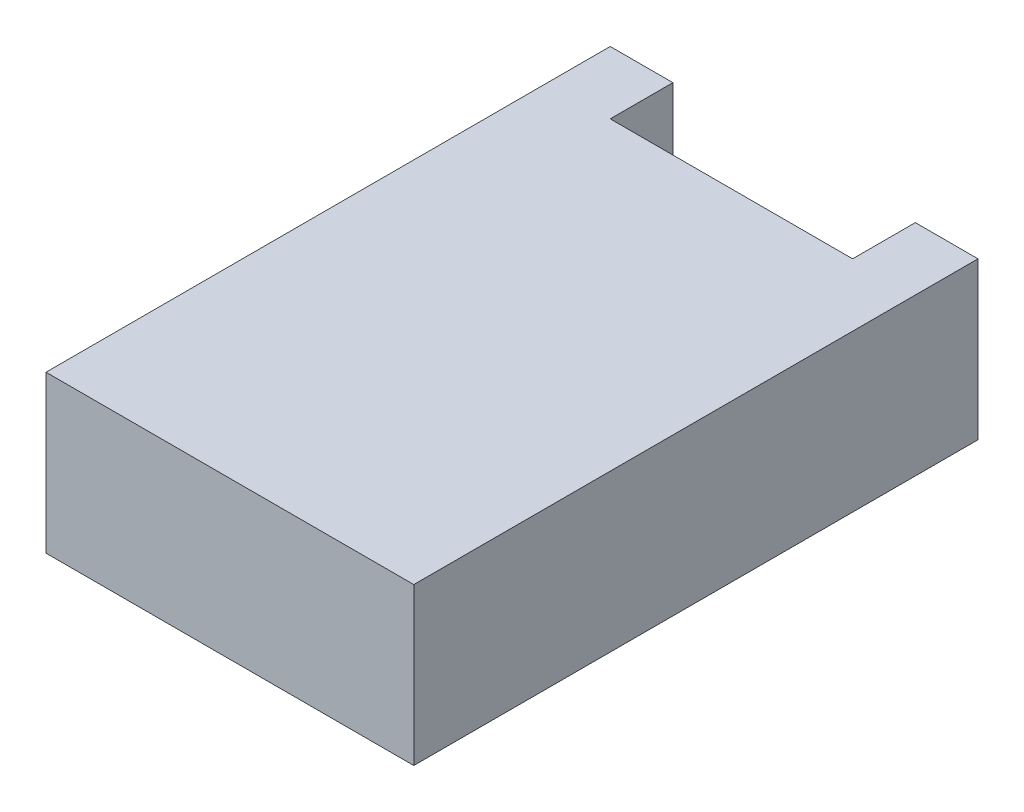
SolidWorks part; units mm, degrees
ref_plane "Front Plane" through (0, 0, 0) normal (0, 0, 1) x (1, 0, 0)
ref_plane "Top Plane" through (0, 0, 0) normal (0, 1, 0) x (1, 0, 0)
ref_plane "Right Plane" through (0, 0, 0) normal (1, 0, 0) x (0, 0, -1)
sketch "Sketch1" plane through (0, 0, 0) normal (0, 1, 0) x (1, 0, 0)
  line L6 (-8.8, -12) -> (8.8, -12)
  line L12 (-8.8, -12) -> (-8.8, 12)
  line L13 (-5.8, 12) -> (5.8, 12)
  line L14 (8.8, -12) -> (8.8, 12)
  line L15 (-8.8, -12) -> (8.8, 12) construction
  line L16 (-8.8, 12) -> (8.8, -12) construction
  line L18 (-8.8, 12) -> (-8.8, 15)
  line L19 (-8.8, 15) -> (-5.8, 15)
  line L20 (-5.8, 12) -> (-5.8, 15)
  line L22 (8.8, 12) -> (8.8, 15)
  line L23 (8.8, 15) -> (5.8, 15)
  line L24 (5.8, 12) -> (5.8, 15)
  point P0 (0, 0)
  dimension "D1" = 24
  dimension "D2" = 17.6
  dimension "D3" = 3
  dimension "D4" = 3
  dimension "D5" = 3
  dimension "D6" = 3
extrude "Boss-Extrude1" add sketch "Sketch1" along normal blind 7.5
